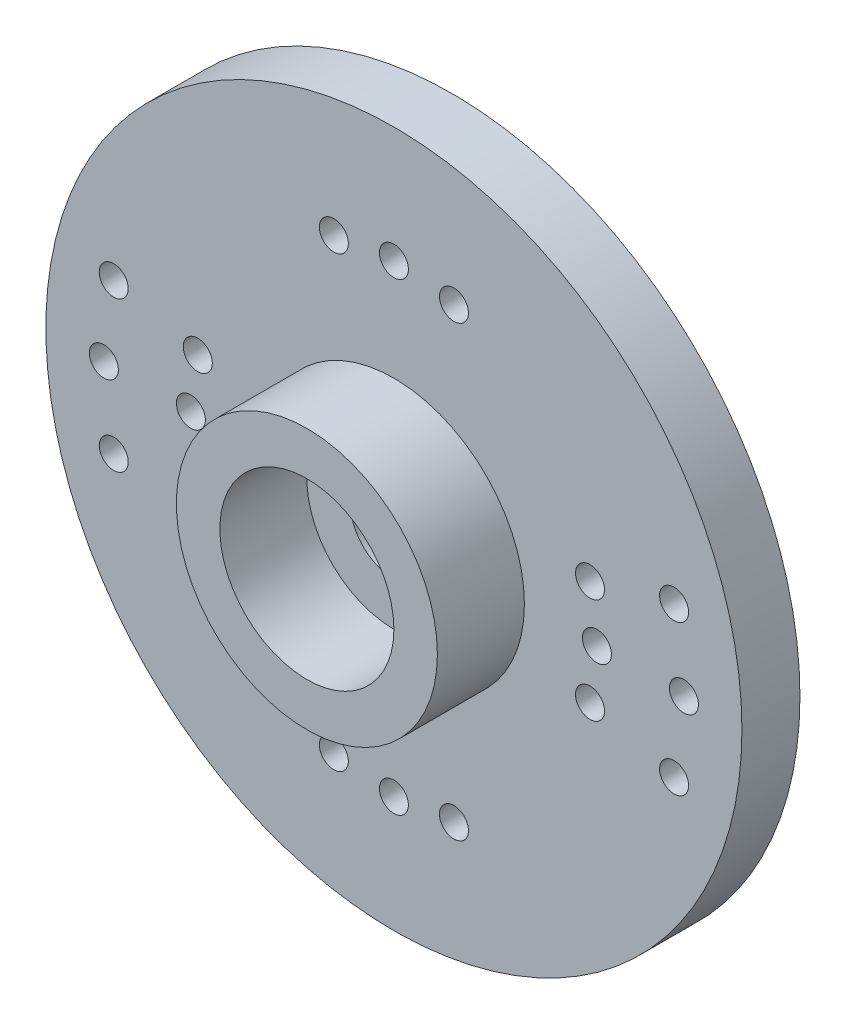
SolidWorks part; units mm, degrees
material "Nylon 101"
ref_plane "Front Plane" through (0, 0, 0) normal (0, 0, 1) x (1, 0, 0)
ref_plane "Top Plane" through (0, 0, 0) normal (0, 1, 0) x (1, 0, 0)
ref_plane "Right Plane" through (0, 0, 0) normal (1, 0, 0) x (0, 0, -1)
sketch "Sketch1" plane through (0, 0, 0) normal (0, 0, 1) x (1, 0, 0)
  circle A0 centre (-46.6929, 3.175) radius 12
extrude "Boss-Extrude1" add sketch "Sketch1" along normal blind 2
sketch "Sketch2" plane through (0, 0, 2) normal (0, 0, 1) x (1, 0, 0)
  circle A0 centre (-46.6929, 3.175) radius 4.5
  circle A1 centre (-46.6929, 3.175) radius 3
extrude "Boss-Extrude2" add sketch "Sketch2" along normal blind 3
sketch "Sketch3" plane through (0, 0, 2) normal (0, 0, 1) x (1, 0, 0)
  circle A0 centre (-46.6929, 3.175) radius 1.5
extrude "Cut-Extrude1" cut sketch "Sketch3" against normal blind 3
sketch "Sketch4" plane through (0, 0, 0) normal (0, 0, -1) x (-1, 0, 0)
  circle A0 centre (46.6929, 3.175) radius 4
  circle A1 centre (46.6929, 3.175) radius 3
  dimension "D1" = 1
extrude "Boss-Extrude3" add sketch "Sketch4" along normal blind 1
sketch "Sketch5" plane through (0, 0, 0) normal (0, 0, -1) x (-1, 0, 0)
  circle A0 centre (46.6929, -4.825) radius 0.5
  circle A1 centre (39.6929, 3.175) radius 0.5
  circle A2 centre (36.6929, 3.175) radius 0.5
  circle A3 centre (53.6929, 3.175) radius 0.5
  circle A4 centre (56.6929, 3.175) radius 0.5
  circle A5 centre (39.9315, 1.3633) radius 0.5
  circle A6 centre (37.0337, 0.5868) radius 0.5
  circle A7 centre (39.9315, 4.9867) radius 0.5
  circle A8 centre (37.0337, 5.7632) radius 0.5
  circle A9 centre (53.4544, 4.9867) radius 0.5
  circle A10 centre (56.3522, 5.7632) radius 0.5
  circle A11 centre (53.4544, 1.3633) radius 0.5
  circle A12 centre (56.3522, 0.5868) radius 0.5
  circle A13 centre (46.6929, 11.175) radius 0.5
  circle A14 centre (44.6224, -4.5524) radius 0.5
  circle A15 centre (48.7635, 10.9024) radius 0.5
  circle A16 centre (48.7635, -4.5524) radius 0.5
  circle A17 centre (44.6224, 10.9024) radius 0.5
  circle A18 centre (46.6929, 3.175) radius 1.5 construction
  dimension "D1" = 2
  dimension "D2" = 8
  dimension "D3" = 2
  dimension "D5" = 2
  dimension "D7" = 2
  dimension "D9" = 2
  dimension "D11" = 2
  dimension "D13" = 2
  dimension "D15" = 2
extrude "Cut-Extrude2" cut sketch "Sketch5" against normal blind 2 contours A16 | A14 | A0 | A5 | A6 | A2 | A1 | A8 | A7 | A17 | A13 | A15 | A9 | A3 | A11 | A12 | A4 | A10
